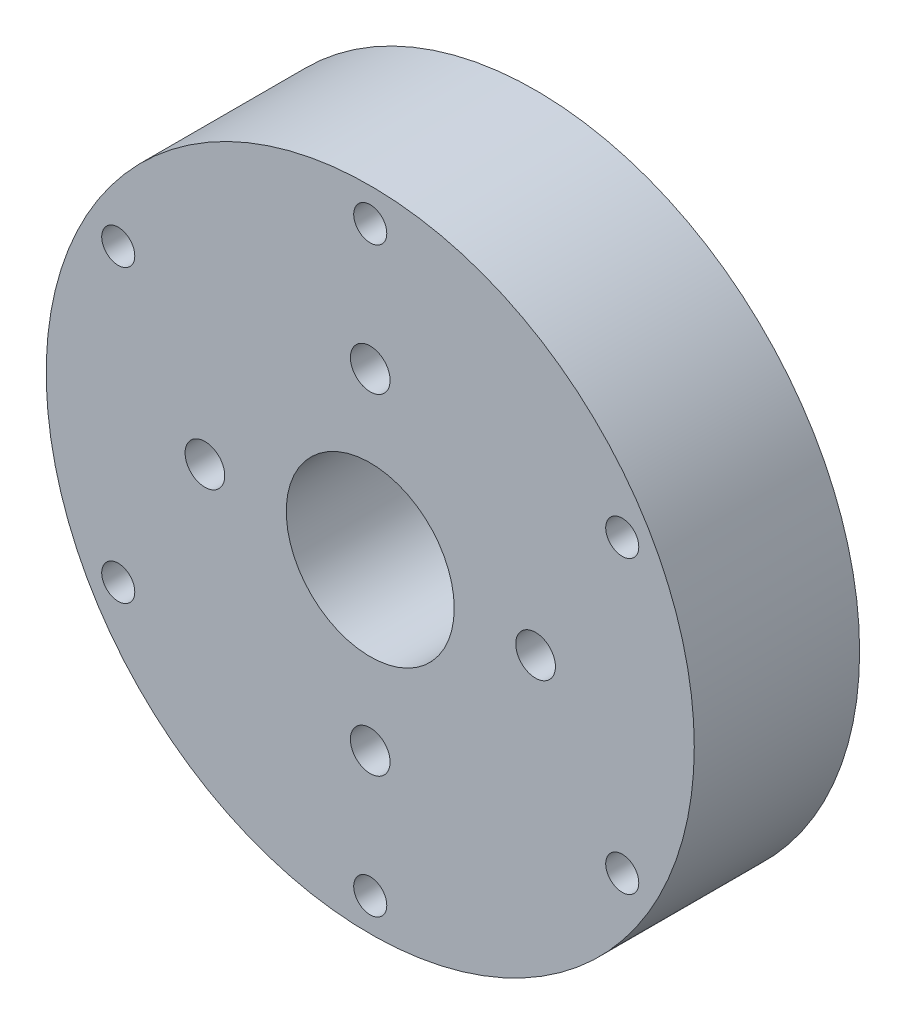
SolidWorks part; units mm, degrees
material "0.6010 (EN-GJL-100)"
ref_plane "前视基准面" through (0, 0, 0) normal (0, 0, 1) x (1, 0, 0)
ref_plane "上视基准面" through (0, 0, 0) normal (0, 1, 0) x (1, 0, 0)
ref_plane "右视基准面" through (0, 0, 0) normal (1, 0, 0) x (0, 0, -1)
sketch "草图1" plane through (0, 0, 0) normal (0, 0, 1) x (1, 0, 0)
  circle A0 centre (0, 0) radius 24.5
  dimension "D1" = 49
extrude "凸台-拉伸1" add sketch "草图1" along normal blind 12.5
sketch "草图2" plane through (0, 0, 12.5) normal (0, 0, 1) x (1, 0, 0)
  line L0 (43.292, 0) -> (-48.2895, 0) construction
  line L1 (0, 36.3075) -> (0, -36.3075) construction
  line L2 (19.0526, 11) -> (0, 0) construction
  line L3 (0, 0) -> (-19.0526, 11) construction
  line L4 (-19.0526, -11) -> (0, 0) construction
  line L5 (0, 0) -> (19.0526, -11) construction
  circle A0 centre (0, 0) radius 22 construction
  circle A2 centre (0, 22) radius 1.25
  circle A3 centre (0, -22) radius 1.25
  circle A4 centre (19.0526, 11) radius 1.25
  circle A5 centre (-19.0526, 11) radius 1.25
  circle A6 centre (19.0526, -11) radius 1.25
  circle A7 centre (-19.0526, -11) radius 1.25
  dimension "D1" = 44
  dimension "D2" = 2.5
  dimension "D3" = 2.5
  dimension "D4" = 2.5
  dimension "D5" = 2.5
  dimension "D6" = 2.5
  dimension "D7" = 2.5
  dimension "D8" = 60
  dimension "D9" = 60
  dimension "D10" = 60
  dimension "D11" = 60
extrude "切除-拉伸1" cut sketch "草图2" against normal blind 3
sketch "草图3" plane through (0, 0, 12.5) normal (0, 0, 1) x (1, 0, 0)
  circle A0 centre (0, 0) radius 12.5 construction
  circle A1 centre (0, 12.5) radius 1.5
  circle A2 centre (0, -12.5) radius 1.5
  circle A3 centre (12.5, 0) radius 1.5
  circle A4 centre (-12.5, 0) radius 1.5
  dimension "D1" = 25
  dimension "D2" = 3
  dimension "D3" = 3
  dimension "D4" = 3
  dimension "D5" = 3
extrude "切除-拉伸2" cut sketch "草图3" against normal blind 3.5
sketch "草图5" plane through (0, 0, 12.5) normal (0, 0, 1) x (1, 0, 0)
  circle A0 centre (0, 0) radius 6.35
  dimension "D1" = 12.7
extrude "切除-拉伸3" cut sketch "草图5" against normal blind 10
